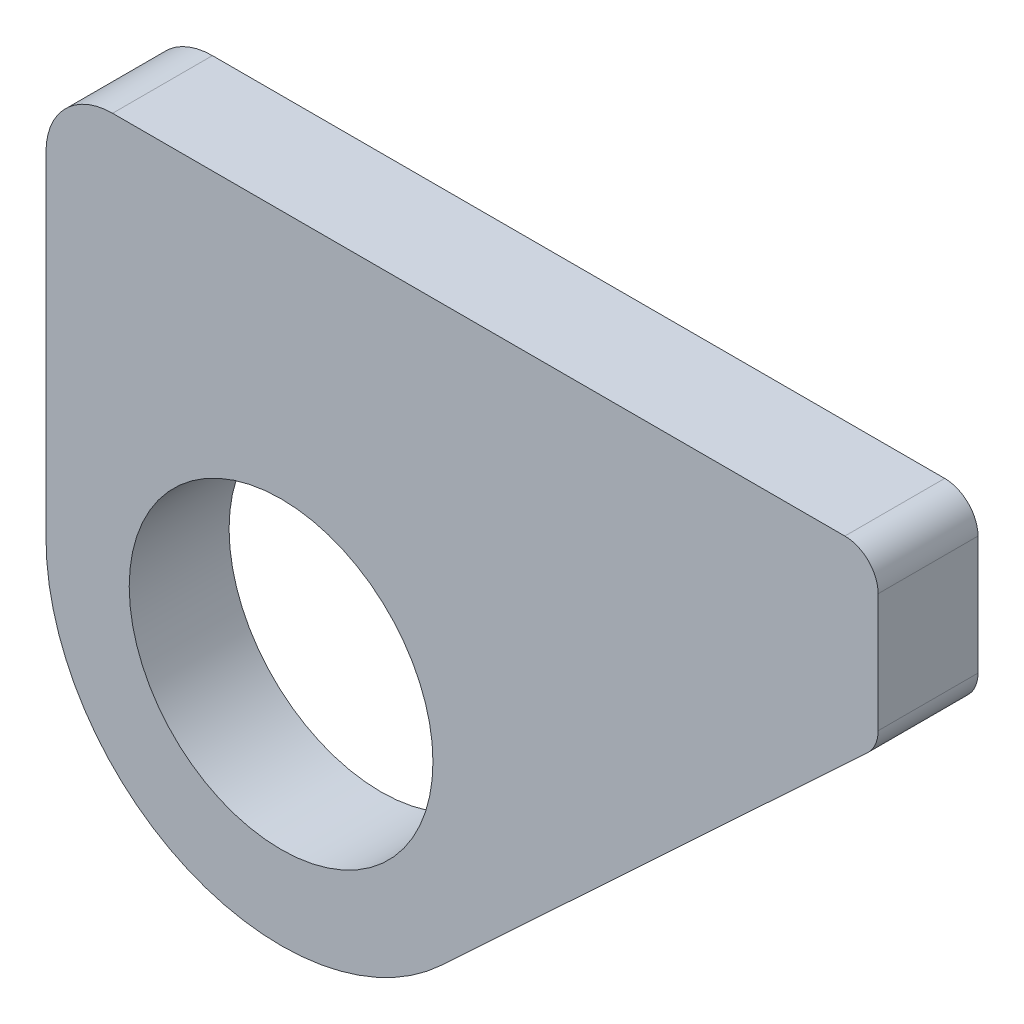
SolidWorks part; units mm, degrees
ref_plane "Front Plane" through (0, 0, 0) normal (0, 0, 1) x (1, 0, 0)
ref_plane "Top Plane" through (0, 0, 0) normal (0, 1, 0) x (1, 0, 0)
ref_plane "Right Plane" through (0, 0, 0) normal (1, 0, 0) x (0, 0, -1)
sketch "Sketch1" plane through (0, 0, 0) normal (0, 0, 1) x (1, 0, 0)
  line L0 (115.1137, 53.4005) -> (108.0512, 53.4005)
  line L1 (108.0512, 53.4005) -> (108.0512, 46.338)
  line L2 (108.0512, 53.4005) -> (108.0512, 58.4005)
  line L3 (108.0512, 58.4005) -> (133.0512, 58.4005)
  line L4 (133.0512, 58.4005) -> (133.0512, 53.4005)
  line L5 (133.0512, 53.4005) -> (119.9286, 41.1713)
  circle A1 centre (115.1137, 46.338) radius 7.0625
  circle A3 centre (115.1137, 46.338) radius 4.5625
  dimension "D3" = 5
  dimension "D4" = 25
  dimension "D2" = 2.5
extrude "Boss-Extrude1" add sketch "Sketch1" along normal blind 3 contours A1 A3 | A1 L0 L1 | A1 L5 L4 L3 L2 L0
fillet "Fillet1" radius 2 1 edges at (108.0512, 58.4005, 1.5)
fillet "Fillet2" radius 1 2 edges at (133.0512, 53.4005, 1.5) (133.0512, 58.4005, 1.5)
